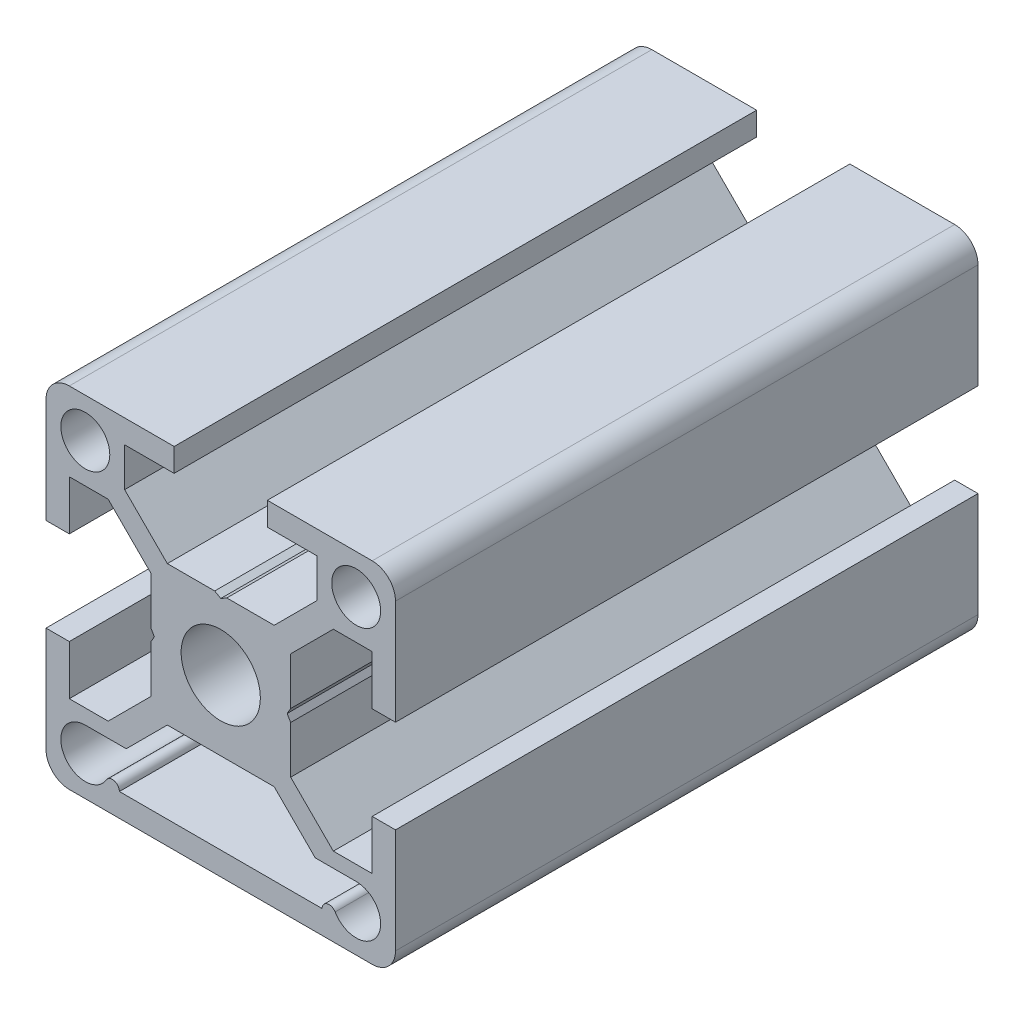
SolidWorks part; units mm, degrees
ref_plane "Front Plane" through (0, 0, 0) normal (0, 0, 1) x (1, 0, 0)
ref_plane "Top Plane" through (0, 0, 0) normal (0, 1, 0) x (1, 0, 0)
ref_plane "Right Plane" through (0, 0, 0) normal (1, 0, 0) x (0, 0, -1)
ref_plane "Plane1" through (0, 0, -50) normal (0, 0, -1) x (-1, 0, 0)
sketch "Sketch1" plane through (0, 0, -50) normal (0, 0, -1) x (-1, 0, 0)
  line L0 (13, 4) -> (15, 4)
  line L1 (15, 4) -> (15, 13)
  line L2 (13, 15) -> (4, 15)
  line L3 (4, 15) -> (4, 13)
  line L4 (4, 13) -> (8.25, 13)
  line L5 (8.25, 13) -> (8.25, 9.6642)
  line L6 (8.25, 9.6642) -> (4.5858, 6)
  line L7 (4.5858, 6) -> (0.5196, 6)
  line L8 (0.5196, 6) -> (0, 5.7)
  line L9 (0, 5.7) -> (-0.5196, 6)
  line L10 (-0.5196, 6) -> (-4.5858, 6)
  line L11 (-4.5858, 6) -> (-8.25, 9.6642)
  line L12 (-8.25, 9.6642) -> (-8.25, 13)
  line L13 (-8.25, 13) -> (-4, 13)
  line L14 (-4, 13) -> (-4, 15)
  line L15 (-4, 15) -> (-13, 15)
  line L16 (-15, 13) -> (-15, 4)
  line L17 (-15, 4) -> (-13, 4)
  line L18 (-13, 4) -> (-13, 8.25)
  line L19 (-13, 8.25) -> (-9.6642, 8.25)
  line L20 (-9.6642, 8.25) -> (-6, 4.5858)
  line L21 (-6, 4.5858) -> (-6, 0.5196)
  line L22 (-6, 0.5196) -> (-5.7, 0)
  line L23 (-5.7, 0) -> (-6, -0.5196)
  line L24 (-6, -0.5196) -> (-6, -4.5858)
  line L25 (-6, -4.5858) -> (-9.6642, -8.25)
  line L26 (-9.6642, -8.25) -> (-13, -8.25)
  line L27 (-13, -8.25) -> (-13, -4)
  line L28 (-13, -4) -> (-15, -4)
  line L29 (-15, -4) -> (-15, -13)
  line L30 (-13, -15) -> (13, -15)
  line L31 (15, -13) -> (15, -4)
  line L32 (15, -4) -> (13, -4)
  line L33 (13, -4) -> (13, -8.25)
  line L34 (13, -8.25) -> (9.6642, -8.25)
  line L35 (9.6642, -8.25) -> (6, -4.5858)
  line L36 (6, -4.5858) -> (6, -0.5196)
  line L37 (6, -0.5196) -> (5.7, 0)
  line L38 (5.7, 0) -> (6, 0.5196)
  line L39 (6, 0.5196) -> (6, 4.5858)
  line L40 (6, 4.5858) -> (9.6642, 8.25)
  line L41 (9.6642, 8.25) -> (13, 8.25)
  line L42 (13, 8.25) -> (13, 4)
  line L43 (8.7013, -13) -> (-8.7013, -13)
  line L44 (-11.625, -9.525) -> (-8.1108, -9.525)
  line L45 (-8.1108, -9.525) -> (-4.5858, -6)
  line L46 (-4.5858, -6) -> (4.5858, -6)
  line L47 (4.5858, -6) -> (8.1108, -9.525)
  line L48 (8.1108, -9.525) -> (11.625, -9.525)
  arc A0 (15, 13) -> (13, 15) centre (13, 13) ccw
  arc A1 (-13, 15) -> (-15, 13) centre (-13, 13) ccw
  arc A2 (-15, -13) -> (-13, -15) centre (-13, -13) ccw
  arc A3 (13, -15) -> (15, -13) centre (13, -13) ccw
  circle A4 centre (0, 0) radius 3.4
  circle A5 centre (-11.625, 11.625) radius 2.1
  circle A6 centre (11.625, 11.625) radius 2.1
  arc A7 (-8.7013, -13) -> (-9.8177, -12.6944) centre (-9.3013, -13) ccw
  arc A8 (-9.8177, -12.6944) -> (-11.625, -9.525) centre (-11.625, -11.625) cw
  arc A9 (11.625, -9.525) -> (9.8177, -12.6944) centre (11.625, -11.625) cw
  arc A10 (9.8177, -12.6944) -> (8.7013, -13) centre (9.3013, -13) ccw
extrude "Extrude1" add sketch "Sketch1" against normal blind 50
